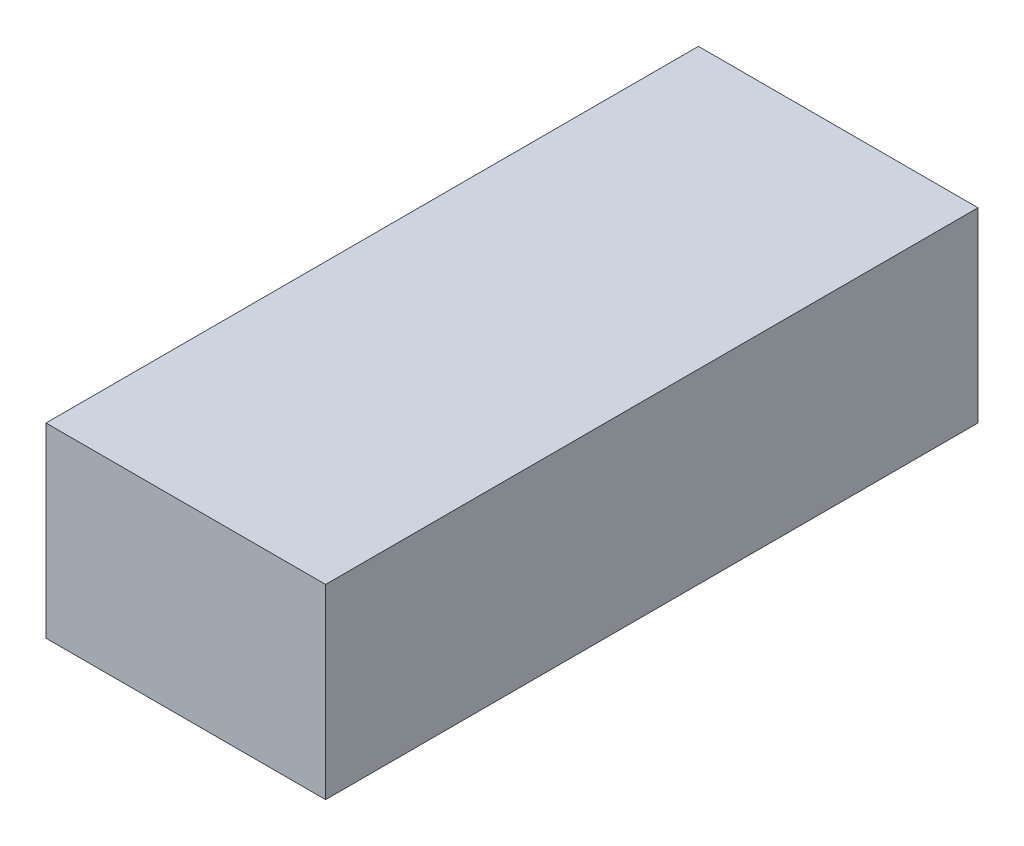
SolidWorks part; units mm, degrees
ref_plane "Front Plane" through (0, 0, 0) normal (0, 0, 1) x (1, 0, 0)
ref_plane "Top Plane" through (0, 0, 0) normal (0, 1, 0) x (1, 0, 0)
ref_plane "Right Plane" through (0, 0, 0) normal (1, 0, 0) x (0, 0, -1)
sketch "Sketch1" plane through (0, 0, 0) normal (0, 1, 0) x (1, 0, 0)
  line L1 (0, 0) -> (30.48, 0)
  line L2 (0, 0) -> (0, 71.12)
  line L3 (0, 71.12) -> (30.48, 71.12)
  line L4 (30.48, 0) -> (30.48, 71.12)
  dimension "D1" = 30.48
  dimension "D2" = 71.12
extrude "Boss-Extrude1" add sketch "Sketch1" along normal blind 20.32
